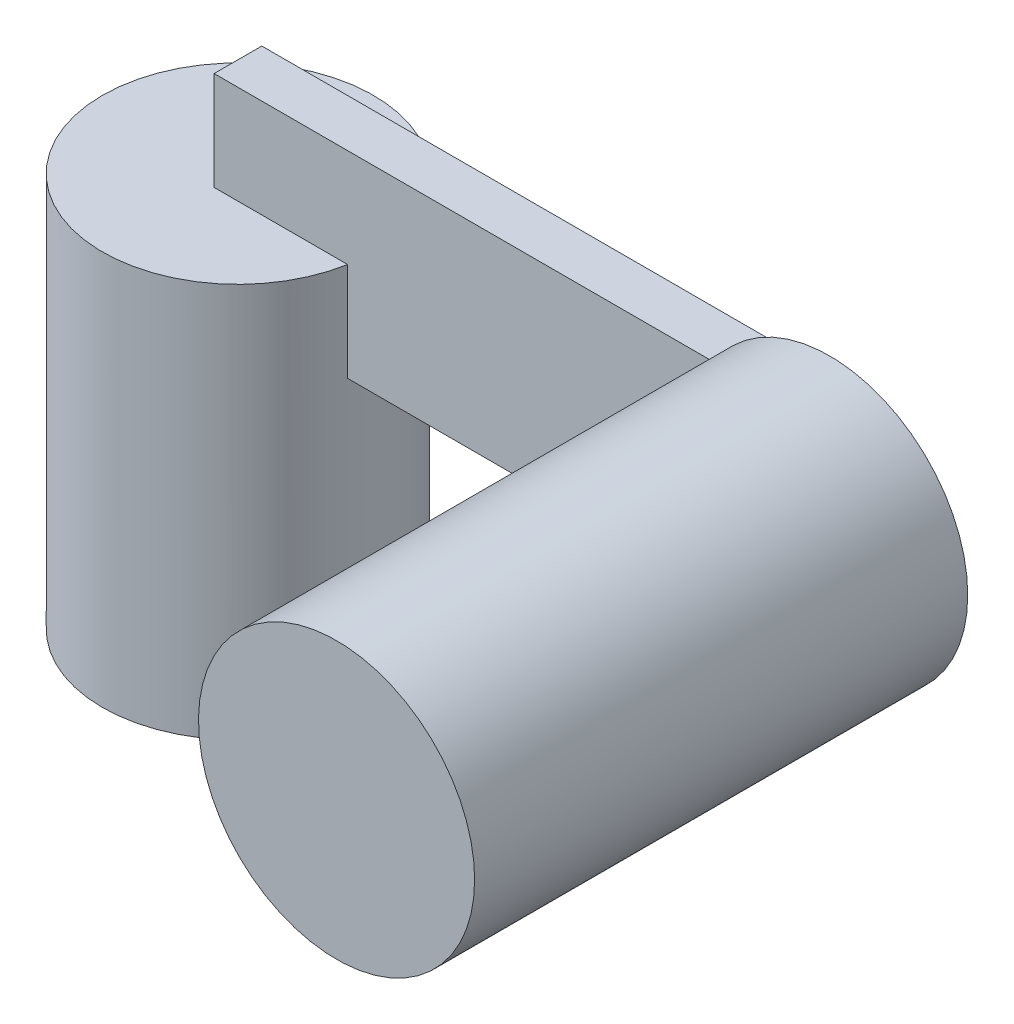
SolidWorks part; units mm, degrees
ref_plane "Front Plane" through (0, 0, 0) normal (0, 0, 1) x (1, 0, 0)
ref_plane "Top Plane" through (0, 0, 0) normal (0, 1, 0) x (1, 0, 0)
ref_plane "Right Plane" through (0, 0, 0) normal (1, 0, 0) x (0, 0, -1)
sketch "Sketch1" plane through (0, 0, 0) normal (0, 1, 0) x (1, 0, 0)
  circle A0 centre (0, 0) radius 6.875
  dimension "D1" = 13.75
extrude "Boss-Extrude1" add sketch "Sketch1" along normal blind 20
sketch "Sketch2" plane through (0, 0, 0) normal (1, 0, 0) x (0, 0, -1)
  line L1 (-1.2088, 25) -> (1.2088, 25)
  line L2 (-1.2088, 25) -> (-1.2088, 15)
  line L3 (-1.2088, 15) -> (1.2088, 15)
  line L4 (1.2088, 25) -> (1.2088, 15)
  line L5 (6.875, 20) -> (-6.875, 20) construction
  point P4 (0, 25)
  dimension "D1" = 2.4176
  dimension "D2" = 10
  dimension "D3" = 5
extrude "Boss-Extrude2" add sketch "Sketch2" along normal blind 30
sketch "Sketch3" plane through (0, 0, 0) normal (0, 0, 1) x (1, 0, 0)
  line L0 (30, 25) -> (30, 15) construction
  circle A0 centre (30, 20) radius 7
  dimension "D1" = 14
extrude "Boss-Extrude3" add sketch "Sketch3" along normal blind 25
